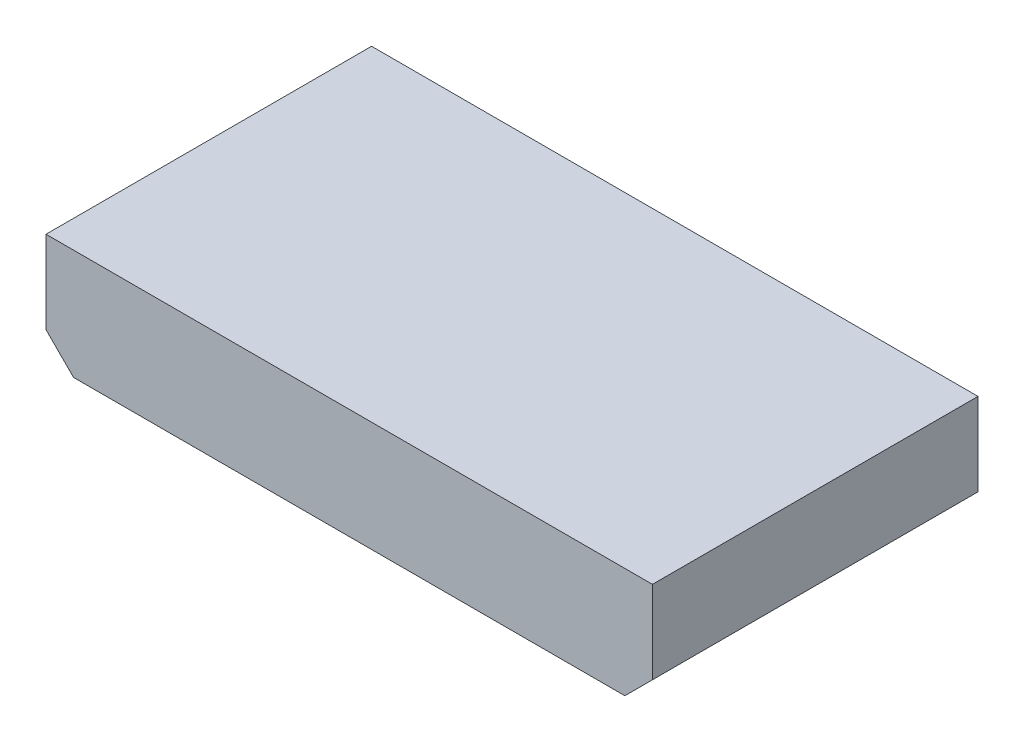
SolidWorks part; units mm, degrees
ref_plane "Front Plane" through (0, 0, 0) normal (0, 0, 1) x (1, 0, 0)
ref_plane "Top Plane" through (0, 0, 0) normal (0, 1, 0) x (1, 0, 0)
ref_plane "Right Plane" through (0, 0, 0) normal (1, 0, 0) x (0, 0, -1)
sketch "Sketch1" plane through (0, 0, 0) normal (0, 0, 1) x (1, 0, 0)
  line L0 (-5.08, 2.54) -> (-5.08, -1.27)
  line L1 (-5.08, -1.27) -> (-3.81, -2.54)
  line L2 (-3.81, -2.54) -> (21.59, -2.54)
  line L3 (21.59, -2.54) -> (22.86, -1.27)
  line L4 (22.86, -1.27) -> (22.86, 2.54)
  line L5 (22.86, 2.54) -> (-5.08, 2.54)
extrude "Component_Outline" add sketch "Sketch1" along normal blind 15 separate body
sketch "Sketch2" plane through (0, 0, 0) normal (0, 0, 1) x (1, 0, 0)
  circle A0 centre (0, 0) radius 0.25
extrude "1" add sketch "Sketch2" against normal blind 2 separate body
sketch "Sketch3" plane through (0, 0, 0) normal (0, 0, 1) x (1, 0, 0)
  circle A0 centre (2.54, 0) radius 0.25
extrude "2" add sketch "Sketch3" against normal blind 2 separate body
sketch "Sketch4" plane through (0, 0, 0) normal (0, 0, 1) x (1, 0, 0)
  circle A0 centre (5.08, 0) radius 0.25
extrude "3" add sketch "Sketch4" against normal blind 2 separate body
sketch "Sketch5" plane through (0, 0, 0) normal (0, 0, 1) x (1, 0, 0)
  circle A0 centre (7.62, 0) radius 0.25
extrude "4" add sketch "Sketch5" against normal blind 2 separate body
sketch "Sketch6" plane through (0, 0, 0) normal (0, 0, 1) x (1, 0, 0)
  circle A0 centre (10.16, 0) radius 0.25
extrude "5" add sketch "Sketch6" against normal blind 2 separate body
sketch "Sketch7" plane through (0, 0, 0) normal (0, 0, 1) x (1, 0, 0)
  circle A0 centre (12.7, 0) radius 0.25
extrude "6" add sketch "Sketch7" against normal blind 2 separate body
sketch "Sketch8" plane through (0, 0, 0) normal (0, 0, 1) x (1, 0, 0)
  circle A0 centre (15.24, 0) radius 0.25
extrude "7" add sketch "Sketch8" against normal blind 2 separate body
sketch "Sketch9" plane through (0, 0, 0) normal (0, 0, 1) x (1, 0, 0)
  circle A0 centre (17.78, 0) radius 0.25
extrude "8" add sketch "Sketch9" against normal blind 2 separate body
sketch3d "3DSketch1"
  line L0 (0, 0, 0) -> (1, 0, 0)
  line L1 (0, 0, 0) -> (0, 1, 0)
  line L2 (0, 0, 0) -> (0, 0, 1)
  point P0 (0, 0, 0)
